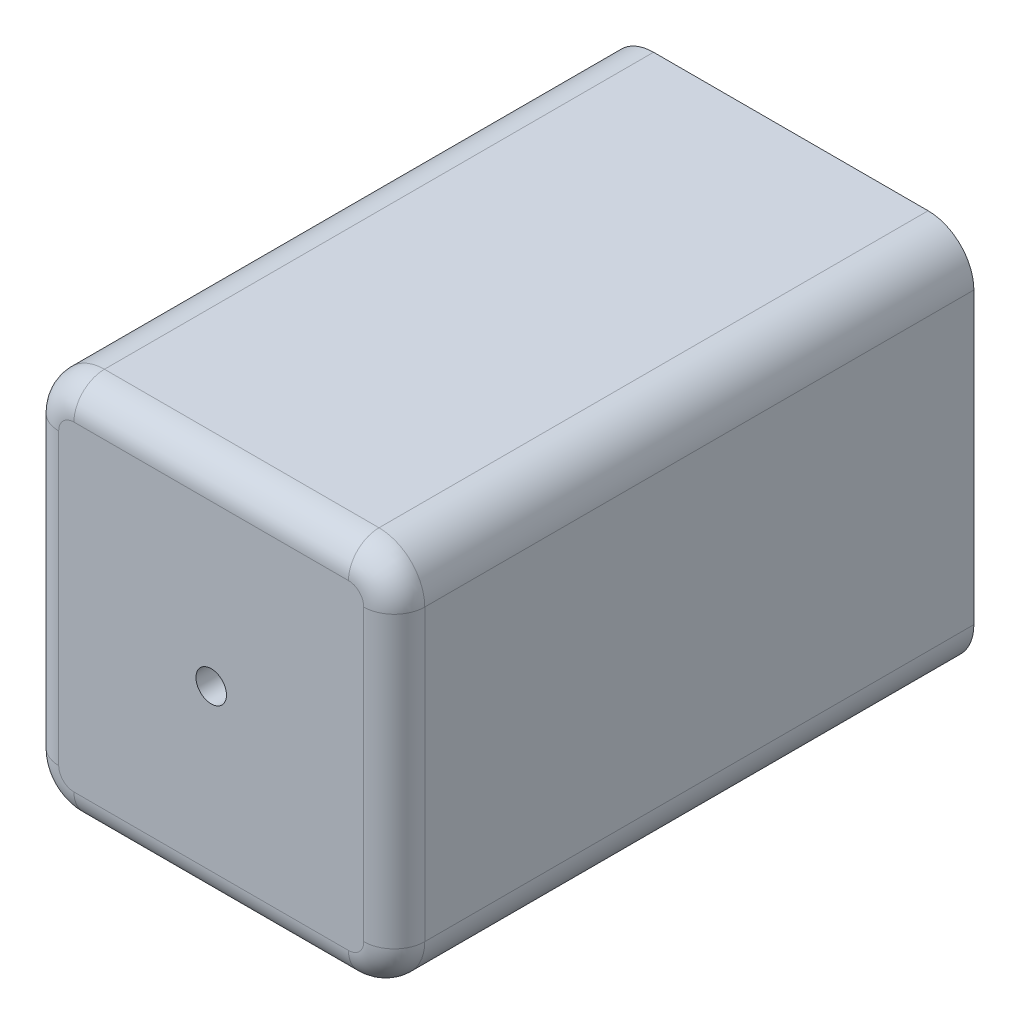
SolidWorks part; units mm, degrees
ref_plane "Piano frontale" through (0, 0, 0) normal (0, 0, 1) x (1, 0, 0)
ref_plane "Piano superiore" through (0, 0, 0) normal (0, 1, 0) x (1, 0, 0)
ref_plane "Piano destro" through (0, 0, 0) normal (1, 0, 0) x (0, 0, -1)
sketch "Schizzo2" plane through (0, 0, 0) normal (1, 0, 0) x (0, 0, -1)
  line L1 (-95, -62.5) -> (95, -62.5)
  line L2 (-95, -62.5) -> (-95, 62.5)
  line L3 (-95, 62.5) -> (95, 62.5)
  line L4 (95, -62.5) -> (95, 62.5)
  line L5 (-95, -62.5) -> (95, 62.5) construction
  line L6 (-95, 62.5) -> (95, -62.5) construction
  point P0 (0, 0)
  dimension "D1" = 190
  dimension "D2" = 125
extrude "Estrusione-Estrusione1" add sketch "Schizzo2" along normal blind 120
sketch "Schizzo3" plane through (0, 0, -95) normal (0, 0, -1) x (-1, 0, 0)
  line L0 (-120, -62.5) -> (0, -62.5) construction
  line L1 (0, -62.5) -> (0, 62.5) construction
  circle A0 centre (-60, 0) radius 5
  dimension "D1" = 10
  dimension "D2" = 62.5
  dimension "D3" = 60
fillet "Raccordo1" radius 15 4 edges at (120, 62.5, 0) (120, -62.5, 0) (0, 62.5, 0) (0, -62.5, 0)
fillet "Raccordo2" radius 10 8 edges at (4.3934, -58.1066, 95) (4.3934, 58.1066, 95) (115.6066, 58.1066, 95) (115.6066, -58.1066, 95) (60, -62.5, 95) (0, 0, 95) (60, 62.5, 95) (120, 0, 95)
extrude "Taglio-Estrusione1" cut sketch "Schizzo3" against normal through all
